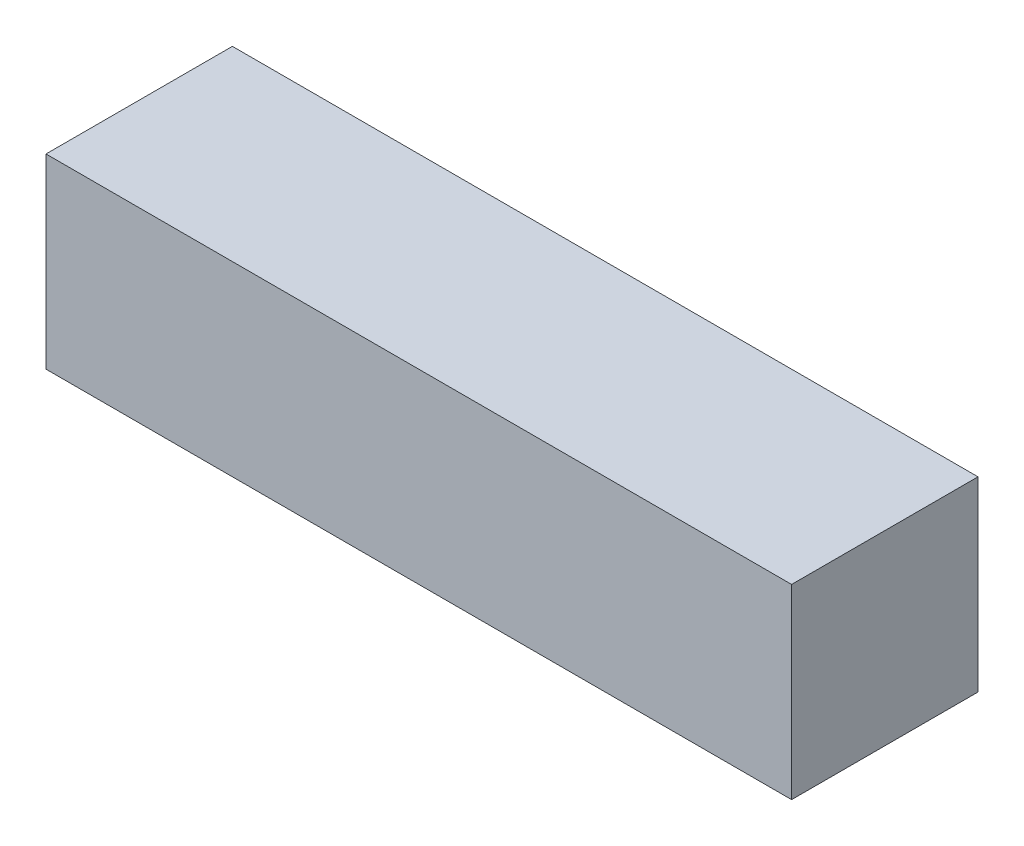
SolidWorks part; units mm, degrees
ref_plane "Front Plane" through (0, 0, 0) normal (0, 0, 1) x (1, 0, 0)
ref_plane "Top Plane" through (0, 0, 0) normal (0, 1, 0) x (1, 0, 0)
ref_plane "Right Plane" through (0, 0, 0) normal (1, 0, 0) x (0, 0, -1)
sketch "Sketch1" plane through (0, 0, 0) normal (0, 1, 0) x (1, 0, 0)
  line L0 (-6.35, 0) -> (6.35, 0) construction
  line L1 (-6.35, 1.5875) -> (6.35, 1.5875)
  line L2 (-6.35, 1.5875) -> (-6.35, -1.5875)
  line L3 (-6.35, -1.5875) -> (6.35, -1.5875)
  line L4 (6.35, 1.5875) -> (6.35, -1.5875)
  dimension "Square Size" = 3.175
  dimension "Length" = 12.7
extrude "Extrude1" add sketch "Sketch1" against normal blind 3.175
sketch "Sketch2" plane through (44.45, 6.35, 1.5875) normal (0, 0, -1) x (-1, 0, 0)
  line L0 (39.6875, -7.9375) -> (49.2125, -7.9375) construction
  line L1 (39.6875, -6.35) -> (49.2125, -6.35)
  line L2 (39.6875, -9.525) -> (49.2125, -9.525)
  line L5 (50.8, -7.9375) -> (49.2125, -7.9375) construction
  line L6 (39.6875, -7.9375) -> (38.1, -7.9375) construction
  line L7 (38.1, -9.525) -> (38.1, -6.35) construction
  line L8 (50.8, -9.525) -> (50.8, -6.35) construction
  line L9 (38.1, -6.35) -> (50.8, -6.35) construction
  arc A0 (39.6875, -6.35) -> (39.6875, -9.525) centre (39.6875, -7.9375) ccw
  arc A1 (49.2125, -9.525) -> (49.2125, -6.35) centre (49.2125, -7.9375) ccw
  point P2 (44.45, -7.9375)
extrude "Extrude2" [suppressed] cut sketch "Sketch2" along normal through all flip side to cut
sketch "Sketch3" plane through (0, 0, 0) normal (0, 1, 0) x (1, 0, 0)
  line L0 (0, -1.5875) -> (0, 1.5875) construction
  line L1 (-6.35, -1.5875) -> (6.35, -1.5875) construction
  line L2 (6.35, 1.5875) -> (-6.35, 1.5875) construction
  dimension "D1" = 3.175
